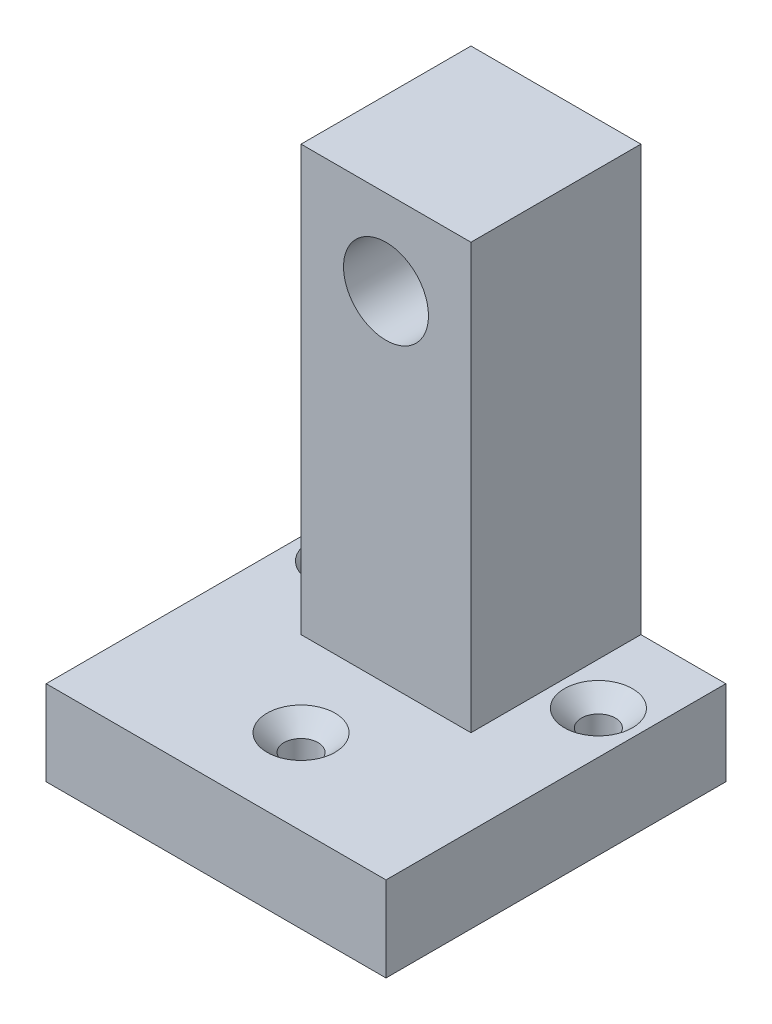
SolidWorks part; units mm, degrees
ref_plane "Plan de face" through (0, 0, 0) normal (0, 0, 1) x (1, 0, 0)
ref_plane "Plan de dessus" through (0, 0, 0) normal (0, 1, 0) x (1, 0, 0)
ref_plane "Plan de droite" through (0, 0, 0) normal (1, 0, 0) x (0, 0, -1)
sketch "Esquisse1" plane through (0, 0, 0) normal (0, 0, 1) x (1, 0, 0)
  line L0 (-4.9542, 0) -> (-0.9542, 0)
  line L1 (-0.9542, 0) -> (-0.9542, 1)
  line L2 (-0.9542, 1) -> (-1.9542, 1)
  line L3 (-1.9542, 1) -> (-1.9542, 6)
  line L4 (-1.9542, 6) -> (-3.9542, 6)
  line L5 (-3.9542, 6) -> (-3.9542, 1)
  line L6 (-3.9542, 1) -> (-4.9542, 1)
  line L7 (-4.9542, 1) -> (-4.9542, 0)
  dimension "D1" = 5
  dimension "D2" = 1
  dimension "D3" = 1
  dimension "D4" = 1
  dimension "D5" = 2
  dimension "D6" = 1
extrude "Boss.-Extru.2" add sketch "Esquisse1" along normal blind 2 contours L5 L6 L7 L0 L1 L2 L3 L4
sketch "Esquisse3" plane through (0, 0, 2) normal (0, 0, 1) x (1, 0, 0)
  line L0 (-3.9542, 1) -> (-1.9542, 1)
  line L1 (-1.9542, 1) -> (-0.9542, 1)
  line L2 (-0.9542, 1) -> (-0.9542, 0)
  line L3 (-0.9542, 0) -> (-4.9542, 0)
  line L4 (-4.9542, 0) -> (-4.9542, 1)
  line L5 (-4.9542, 1) -> (-3.9542, 1)
extrude "Boss.-Extru.3" add sketch "Esquisse3" along normal blind 2
sketch "Esquisse4" plane through (0, 0, 2) normal (0, 0, 1) x (1, 0, 0)
  line L0 (-3.9542, 6) -> (-3.9542, 1) construction
  line L2 (-1.9542, 6) -> (-3.9542, 6) construction
  circle A0 centre (-2.9542, 5) radius 0.5
  dimension "D1" = 1
  dimension "D2" = 1
  dimension "D3" = 1
extrude "Enlèv. mat.-Extru.1" cut sketch "Esquisse4" against normal blind 2
sketch "Esquisse5" plane through (-3.9542, 0, 0) normal (-1, 0, 0) x (0, 0, 1)
  line L0 (2, 6) -> (2, 1) construction
  line L1 (2, 6) -> (0, 6) construction
  circle A0 centre (1, 5) radius 0.2
  dimension "D1" = 0.4
  dimension "D2" = 1
  dimension "D3" = 1
extrude "Enlèv. mat.-Extru.2" cut sketch "Esquisse5" against normal blind 1
sketch "Esquisse6" plane through (0, 1, 0) normal (0, 1, 0) x (1, 0, 0)
  line L0 (-3.9542, 0) -> (-4.9542, 0) construction
  line L1 (-4.9542, -4) -> (-4.9542, 0) construction
  line L2 (-0.9542, 0) -> (-1.9542, 0) construction
  line L3 (-0.9542, -4) -> (-0.9542, 0) construction
  line L4 (-0.9542, -4) -> (-4.9542, -4) construction
  circle A0 centre (-4.4542, -1) radius 0.2
  circle A1 centre (-1.4542, -1) radius 0.2
  circle A2 centre (-2.9542, -3) radius 0.2
  dimension "D1" = 0.4
  dimension "D2" = 0.4
  dimension "D3" = 0.4
  dimension "D4" = 1
  dimension "D5" = 0.5
  dimension "D6" = 1
  dimension "D7" = 0.5
  dimension "D8" = 1
  dimension "D9" = 2
extrude "Enlèv. mat.-Extru.3" cut sketch "Esquisse6" against normal blind 1
chamfer "Chanfrein1" distance 0.2 angle 45 1 edges at (-3.1542, 1, 3)
chamfer "Chanfrein2" distance 0.2 angle 45 1 edges at (-1.6542, 1, 1)
chamfer "Chanfrein3" distance 0.2 angle 45 1 edges at (-4.6542, 1, 1)
sketch "Esquisse7" plane through (0, 0, 0) normal (0, -1, 0) x (1, 0, 0)
  line L0 (-2.9542, 0) -> (-2.9542, 4) construction
  line L1 (-4.9542, 0) -> (-0.9542, 0) construction
  line L2 (-4.9542, 4) -> (-0.9542, 4) construction
